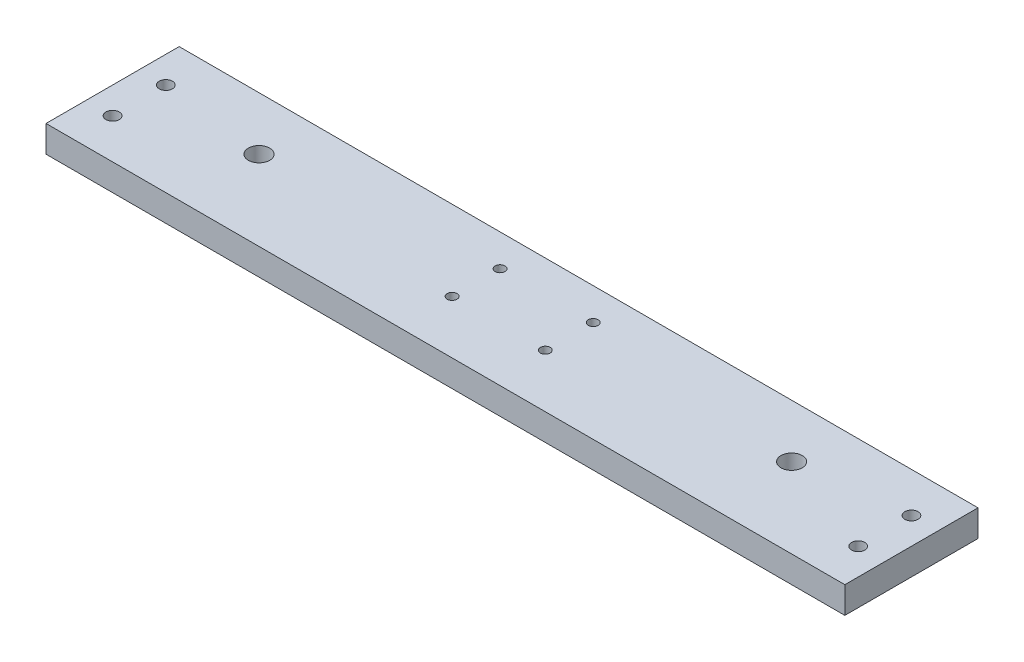
SolidWorks part; units mm, degrees
ref_plane "Front Plane" through (0, 0, 0) normal (0, 0, 1) x (1, 0, 0)
ref_plane "Top Plane" through (0, 0, 0) normal (0, 1, 0) x (1, 0, 0)
ref_plane "Right Plane" through (0, 0, 0) normal (1, 0, 0) x (0, 0, -1)
sketch "Sketch1" plane through (0, 0, 0) normal (0, 1, 0) x (1, 0, 0)
  line L0 (0, 20) -> (0, 0) construction
  line L1 (150, -30) -> (-150, -30)
  line L2 (150, -30) -> (150, 20)
  line L3 (150, 20) -> (-150, 20)
  line L4 (-150, -30) -> (-150, 20)
  line L5 (150, -30) -> (-150, 20) construction
  line L6 (150, 20) -> (-150, -30) construction
  line L7 (0, 0) -> (-100, 0) construction
  circle A0 centre (-100, 0) radius 4
  circle A1 centre (100, 0) radius 4
  point P0 (0, -5)
  dimension "D3" = 8
  dimension "D1" = 50
  dimension "D2" = 300
  dimension "D4" = 200
  dimension "D5" = 5
extrude "main" add sketch "Sketch1" along normal blind 10
sketch "Sketch4" plane through (0, 10, 0) normal (0, 1, 0) x (1, 0, 0)
  line L0 (0, 20) -> (0, -5) construction
  line L1 (150, 20) -> (-150, 20) construction
  line L2 (0, -5) -> (-150, -5) construction
  line L3 (-150, 20) -> (-150, -30) construction
  circle A0 centre (-140, 5) radius 2.5
  circle A1 centre (-140, -15) radius 2.5
  circle A2 centre (140, -15) radius 2.5
  circle A3 centre (140, 5) radius 2.5
  dimension "D1" = 5
  dimension "D2" = 10
  dimension "D3" = 20
extrude "mount" cut sketch "Sketch4" against normal through all
sketch "Sketch3" plane through (0, 10, 0) normal (0, 1, 0) x (1, 0, 0)
  line L0 (0, 20) -> (0, -1) construction
  line L1 (150, 20) -> (-150, 20) construction
  line L2 (0, -1) -> (-22.9552, -1) construction
  circle A0 centre (0, -1) radius 8.5 construction
  circle A1 centre (-17.5, 8) radius 1.85
  circle A2 centre (17.5, 8) radius 1.85
  circle A3 centre (-17.5, -10) radius 1.85
  circle A4 centre (17.5, -10) radius 1.85
  point P2 (-100, 0)
  dimension "D1" = 17
  dimension "D5" = 3.7
  dimension "D2" = 1
  dimension "D3" = 35
  dimension "D4" = 18
extrude "bearing_mount" cut sketch "Sketch3" against normal through all
sketch "Sketch2" plane through (0, 10, 0) normal (0, 1, 0) x (1, 0, 0)
  line L0 (0, -30) -> (0, -1) construction
  line L2 (-150, -30) -> (150, -30) construction
  line L4 (0, -1) -> (-150, -1) construction
  line L5 (-150, 20) -> (-150, -30) construction
  circle A6 centre (0, -1) radius 11
  circle A7 centre (15.5, -16.5) radius 1.5
  circle A8 centre (-15.5, -16.5) radius 1.5
  circle A9 centre (-15.5, 14.5) radius 1.5
  circle A10 centre (15.5, 14.5) radius 1.5
  point P17 (-100, 0)
  dimension "D1" = 1
  dimension "D4" = 31
  dimension "D2" = 22
  dimension "D3" = 3
  dimension "D5" = 31
extrude "stepper_mount" [suppressed] cut sketch "Sketch2" against normal through all
sketch "Sketch5" [suppressed] plane through (0, 0, 0) normal (0, -1, 0) x (1, 0, 0)
  line L0 (0, 30) -> (0, 1) construction
  line L1 (-150, 30) -> (150, 30) construction
  line L2 (0, 1) -> (-24.4243, 1) construction
  circle A0 centre (-15.5, 16.5) radius 2.75
  circle A1 centre (15.5, 16.5) radius 2.75
  circle A2 centre (15.5, -14.5) radius 2.75
  circle A3 centre (-15.5, -14.5) radius 2.75
  circle A4 centre (-15.5, 16.5) radius 1.5 construction
  dimension "D1" = 5.5
  dimension "D2" = 31
extrude "Cut-Extrude1" [suppressed] cut sketch "Sketch5" against normal blind 3
